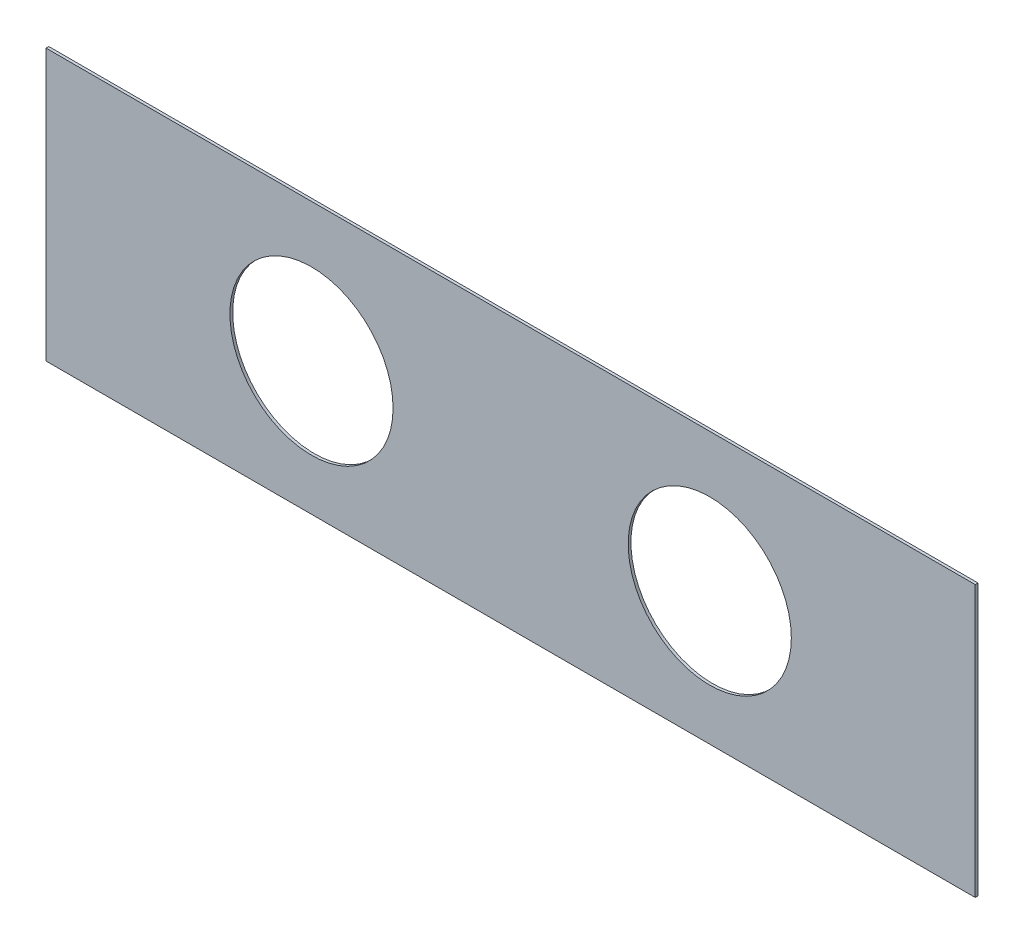
SolidWorks part; units mm, degrees
ref_plane "Front Plane" through (0, 0, 0) normal (0, 0, 1) x (1, 0, 0)
ref_plane "Top Plane" through (0, 0, 0) normal (0, 1, 0) x (1, 0, 0)
ref_plane "Right Plane" through (0, 0, 0) normal (1, 0, 0) x (0, 0, -1)
sketch "Sketch1" plane through (0, 0, 0) normal (0, 0, 1) x (1, 0, 0)
  line L1 (-533.4, 155.575) -> (533.4, 155.575)
  line L2 (-533.4, 155.575) -> (-533.4, -155.575)
  line L3 (-533.4, -155.575) -> (533.4, -155.575)
  line L4 (533.4, 155.575) -> (533.4, -155.575)
  line L5 (-533.4, 155.575) -> (533.4, -155.575) construction
  line L6 (-533.4, -155.575) -> (533.4, 155.575) construction
  point P0 (0, 0)
  dimension "D1" = 1066.8
  dimension "D2" = 311.15
extrude "Boss-Extrude1" add sketch "Sketch1" along normal blind 3.175
sketch "Sketch2" plane through (0, 0, 3.175) normal (0, 0, 1) x (1, 0, 0)
  line L0 (-228.6, -3.175) -> (228.6, -3.175) construction
  line L1 (0, -3.175) -> (0, -155.575) construction
  line L2 (-533.4, -155.575) -> (533.4, -155.575) construction
  circle A0 centre (228.6, -3.175) radius 93.6625
  circle A1 centre (-228.6, -3.175) radius 93.6625
  dimension "D1" = 187.325
  dimension "D2" = 457.2
  dimension "D3" = 152.4
extrude "Cut-Extrude1" cut sketch "Sketch2" against normal up to next
